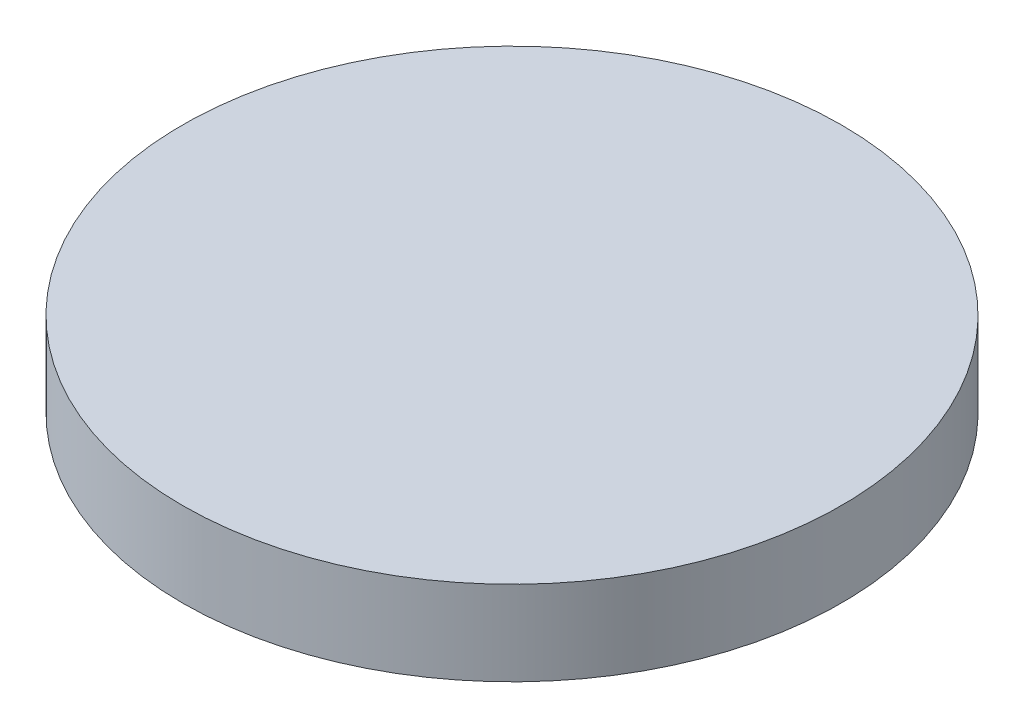
SolidWorks part; units mm, degrees
ref_plane "Front Plane" through (0, 0, 0) normal (0, 0, 1) x (1, 0, 0)
ref_plane "Top Plane" through (0, 0, 0) normal (0, 1, 0) x (1, 0, 0)
ref_plane "Right Plane" through (0, 0, 0) normal (1, 0, 0) x (0, 0, -1)
sketch "Sketch1" plane through (0, 0, 0) normal (0, 1, 0) x (1, 0, 0)
  circle A0 centre (0, 0) radius 24.765
  dimension "D1" = 49.53
extrude "Boss-Extrude1" add sketch "Sketch1" along normal blind 6.35
